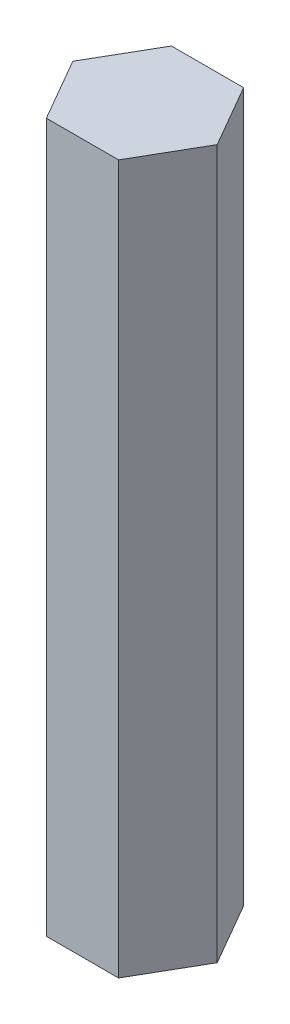
SolidWorks part; units mm, degrees
ref_plane "Front Plane" through (0, 0, 0) normal (0, 0, 1) x (1, 0, 0)
ref_plane "Top Plane" through (0, 0, 0) normal (0, 1, 0) x (1, 0, 0)
ref_plane "Right Plane" through (0, 0, 0) normal (1, 0, 0) x (0, 0, -1)
sketch "Sketch1" plane through (0, 0, 0) normal (0, 1, 0) x (1, 0, 0)
  line L0 (0, 0) -> (7.3323, 0) construction
  line L1 (7.3323, 0) -> (3.6662, 6.35)
  line L2 (3.6662, 6.35) -> (-3.6662, 6.35)
  line L3 (-3.6662, 6.35) -> (-7.3323, 0)
  line L4 (-7.3323, 0) -> (-3.6662, -6.35)
  line L5 (-3.6662, -6.35) -> (3.6662, -6.35)
  line L6 (3.6662, -6.35) -> (7.3323, 0)
  circle A0 centre (0, 0) radius 6.35 construction
  dimension "D1" = 12.7
extrude "Boss-Extrude1" add sketch "Sketch1" along normal blind 71.9582
